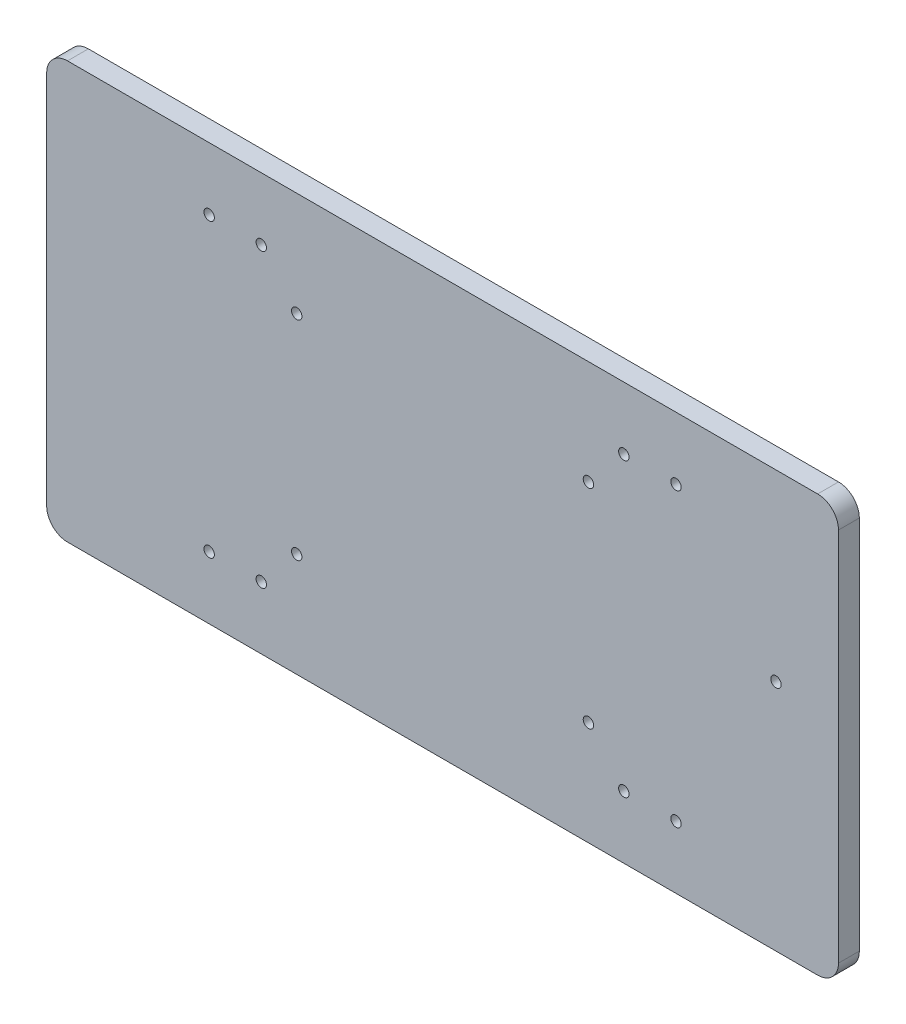
SolidWorks part; units mm, degrees
ref_plane "Front Plane" through (0, 0, 0) normal (0, 0, 1) x (1, 0, 0)
ref_plane "Top Plane" through (0, 0, 0) normal (0, 1, 0) x (1, 0, 0)
ref_plane "Right Plane" through (0, 0, 0) normal (1, 0, 0) x (0, 0, -1)
sketch "Sketch1" plane through (0, 0, 0) normal (0, 0, 1) x (1, 0, 0)
  line L0 (-95, 50) -> (95, 50)
  line L1 (95, 50) -> (95, -50)
  line L2 (95, -50) -> (-95, -50)
  line L3 (-95, 50) -> (-95, -50)
  line L4 (-35, 25) -> (35, 25)
  line L5 (35, 25) -> (35, -25)
  line L6 (35, -25) -> (-35, -25)
  line L7 (-35, -25) -> (-35, 25)
  line L8 (-95, 50) -> (95, -50) construction
  line L9 (-95, -50) -> (95, 50) construction
  line L10 (-35, -25) -> (35, 25) construction
  line L11 (-35, 25) -> (35, -25) construction
  line L12 (80, 50) -> (80, -50) construction
  line L13 (0, 0) -> (0, 14.4751) construction
  line L14 (0, 14.4751) -> (0, 0) construction
  line L15 (0, 0) -> (15.6168, 0) construction
  circle A0 centre (-35, 25) radius 1.25
  circle A2 centre (35, -25) radius 1.25
  circle A4 centre (-35, -25) radius 1.25
  circle A5 centre (35, 25) radius 1.25
  circle A6 centre (80, 5.9699) radius 1.25
  circle A7 centre (-43.5, -35) radius 1.25
  circle A8 centre (-56.0093, -35) radius 1.25
  circle A9 centre (-56.0093, 35) radius 1.25
  circle A10 centre (-43.5, 35) radius 1.25
  circle A11 centre (43.5, -35) radius 1.25
  circle A12 centre (56.0093, -35) radius 1.25
  circle A13 centre (43.5, 35) radius 1.25
  circle A14 centre (56.0093, 35) radius 1.25
  point P8 (0, 0)
  point P10 (0, 0)
  dimension "D6" = 2.5
  dimension "D7" = 2.5
  dimension "D1" = 190
  dimension "D2" = 100
  dimension "D3" = 70
  dimension "D4" = 50
  dimension "D5" = 15
  dimension "D8" = 43.5
  dimension "D9" = 15
extrude "Boss-Extrude2" add sketch "Sketch1" along normal blind 5 contours L0 L3 L2 L1 A14 A13 A11 A9 A8 A7 A6 A5 L5 A2 L6 A4 L7 A0 L4 A10 A12 | A5 L4 A0 L7 A4 L6 A2 L5
fillet "Fillet1" radius 5 4 edges at (-95, -50, 2.5) (95, -50, 2.5) (95, 50, 2.5) (-95, 50, 2.5)
